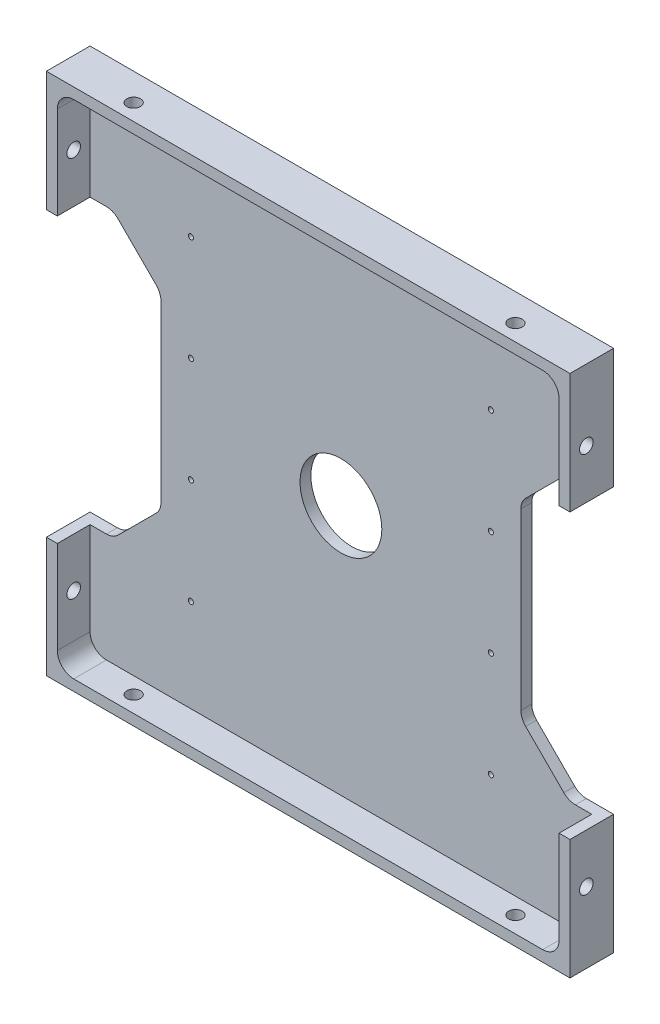
SolidWorks part; units mm, degrees
material "6061-T6 (SS)"
ref_plane "Front" through (0, 0, 0) normal (0, 0, 1) x (1, 0, 0)
ref_plane "Top" through (0, 0, 0) normal (0, 1, 0) x (1, 0, 0)
ref_plane "Right" through (0, 0, 0) normal (1, 0, 0) x (0, 0, -1)
sketch "Sketch1" plane through (0, 0, 0) normal (0, 0, 1) x (1, 0, 0)
  line L1 (-48, -48) -> (48, -48)
  line L2 (-48, -48) -> (-48, 48)
  line L3 (-48, 48) -> (48, 48)
  line L4 (48, -48) -> (48, 48)
  line L5 (-48, -48) -> (48, 48) construction
  line L6 (-48, 48) -> (48, -48) construction
  point P0 (0, 0)
  dimension "D1" = 96
  dimension "D2" = 96
extrude "Boss-Extrude1" add sketch "Sketch1" along normal blind 8
sketch "Sketch2" plane through (0, 0, 8) normal (0, 0, 1) x (1, 0, 0)
  line L1 (46, -46) -> (-46, -46)
  line L2 (46, -46) -> (46, 46)
  line L3 (46, 46) -> (-46, 46)
  line L4 (-46, -46) -> (-46, 46)
  line L5 (46, -46) -> (-46, 46) construction
  line L6 (46, 46) -> (-46, -46) construction
  point P0 (0, 0)
  dimension "D1" = 92
  dimension "D2" = 92
extrude "Component Platform" cut sketch "Sketch2" against normal blind 6
sketch "Sketch3" plane through (0, 0, 2) normal (0, 0, 1) x (1, 0, 0)
  line L1 (-40.8787, -25.1213) -> (-33.8787, -18.1213)
  line L2 (-40.8787, 25.1213) -> (-33.8787, 18.1213)
  line L3 (-33, -16) -> (-33, 16)
  line L4 (-48, -26) -> (-43, -26)
  line L7 (-48, 48) -> (-48, -48) construction
  line L8 (0, -56.7987) -> (0, 73.4321) construction
  line L9 (46, -46) -> (-57.8147, 57.8147) construction
  line L18 (46, 46) -> (-68.5705, -68.5705) construction
  line L23 (-48, 26) -> (-43, 26)
  line L26 (-48, -26) -> (-48, 26)
  line L28 (-48, -48) -> (48, -48) construction
  line L29 (48, -26) -> (48, 26)
  line L30 (48, 26) -> (43, 26)
  line L31 (40.8787, 25.1213) -> (33.8787, 18.1213)
  line L32 (33, -16) -> (33, 16)
  line L33 (40.8787, -25.1213) -> (33.8787, -18.1213)
  line L34 (48, -26) -> (43, -26)
  arc A3 (-33.8787, -18.1213) -> (-33, -16) centre (-36, -16) ccw
  arc A4 (-33.8787, 18.1213) -> (-33, 16) centre (-36, 16) cw
  arc A13 (-40.8787, -25.1213) -> (-43, -26) centre (-43, -23) cw
  arc A15 (-40.8787, 25.1213) -> (-43, 26) centre (-43, 23) ccw
  arc A17 (40.8787, 25.1213) -> (43, 26) centre (43, 23) cw
  arc A18 (33.8787, 18.1213) -> (33, 16) centre (36, 16) ccw
  arc A19 (33.8787, -18.1213) -> (33, -16) centre (36, -16) cw
  arc A20 (40.8787, -25.1213) -> (43, -26) centre (43, -23) ccw
  point P0 (-48, 0)
  point P37 (-48, 0)
  dimension "D2" = 3
  dimension "D3" = 3
  dimension "D4" = 15
  dimension "D6" = 3
  dimension "D7" = 3
  dimension "D8" = 135
  dimension "D5" = 52
  dimension "D9" = 135
  dimension "D10" = 5
  dimension "D11" = 5
  dimension "D12" = 48
extrude "Cable Slots" cut sketch "Sketch3" against normal mid plane 12
sketch "Sketch4" plane through (0, 0, 2) normal (0, 0, 1) x (1, 0, 0)
  circle A0 centre (0, 0) radius 7.5
  dimension "D1" = 15
extrude "Center Mass Cut" cut sketch "Sketch4" against normal blind 6
ref_plane "Center Y-Plane" through (0, 0, 0) normal (1, 0, 0) x (0, 0, -1)
ref_plane "Center X-Plane" through (0, 0, 0) normal (0, -1, 0) x (-1, 0, 0)
fillet "Inner Corner Fillets" radius 3 4 edges at (46, -46, 5) (-46, -46, 5) (46, 46, 5) (-46, 46, 5)
sketch "Sketch8" plane through (48, 0, 0) normal (1, 0, 0) x (0, 0, -1)
  line L0 (-5, -48) -> (-5, 48) construction
  line L1 (-8, -48) -> (0, -48) construction
  line L2 (-8, 48) -> (0, 48) construction
  line L3 (-8, -48) -> (-8, -26) construction
  point P12 (-5, 35)
  point P13 (-5, -35)
  dimension "D1" = 3
  dimension "D2" = 13
  dimension "D3" = 83
sketch "Sketch11" plane through (0, -48, 0) normal (0, -1, 0) x (-1, 0, 0)
  line L0 (48, -5) -> (-48.0639, -5) construction
  line L1 (48, -8) -> (48, 0) construction
  line L2 (48, -8) -> (-48, -8) construction
  dimension "D1" = 3
hole_wizard "Tap Drill for M3x0.5 Tap4" positions "Sketch12" profile "Sketch13" hole size "M3x0.5" standard "ANSI Metric" end condition up to next
sketch "Sketch12" plane through (0, -48, 0) normal (0, -1, 0) x (-1, 0, 0)
  line L0 (48, -5) -> (-48.0639, -5) construction
  point P0 (35, -5)
  point P4 (-35, -5)
  dimension "D1" = 70
  dimension "D2" = 35
sketch "Sketch13" plane through (-35, -48, 5) normal (1, 0, 0) x (0, 0, -1)
  line L0 (0, 0) -> (0, 2)
  line L1 (0, 2) -> (1.25, 2)
  line L2 (1.25, 2) -> (1.25, 0)
  line L5 (1.25, 0) -> (0, 0)
  line L11 (0, -6.35) -> (0, 107.95) construction
  dimension "Thru Hole Dia." = 2.5
  dimension "Thru Hole Depth" = 2
mirror "Mirror2" about plane through (0, 0, 0) normal (0, -1, 0) of "Tap Drill for M3x0.5 Tap4"
sketch "Sketch14" plane through (0, 0, 2) normal (0, 0, 1) x (1, 0, 0)
  line L2 (-34.3786, 28.95) -> (20.4987, 28.95) construction
  line L4 (-27.5, 33.479) -> (-27.5, -23.7116) construction
  line L5 (0, 0) -> (0, 28.95) construction
  point P7 (-27.5, 28.95)
  point P8 (-27.5, -9.65)
  point P9 (-27.5, 9.65)
  point P11 (-27.5, -28.95)
  point P13 (27.5, -28.95)
  point P14 (27.5, -9.65)
  point P15 (27.5, 9.65)
  point P16 (27.5, 28.95)
  dimension "D1" = 27.5
  dimension "D2" = 28.95
  dimension "D3" = 19.3
  dimension "D4" = 19.3
  dimension "D5" = 19.3
hole_wizard "Tap Drill for M1.2x0.25 Tap1" positions "Sketch15" profile "Sketch17" hole size "M1.2x0.25" standard "ANSI Metric" end condition through all
sketch "Sketch15" plane through (0, 0, 2) normal (0, 0, 1) x (1, 0, 0)
  point P0 (-27.5, 28.95)
  point P3 (-27.5, 9.65)
  point P6 (-27.5, -9.65)
  point P9 (-27.5, -28.95)
  point P12 (27.5, -28.95)
  point P15 (27.5, -9.65)
  point P18 (27.5, 9.65)
  point P21 (27.5, 28.95)
sketch "Sketch17" plane through (-27.5, 28.95, 2) normal (1, 0, 0) x (0, -1, 0)
  line L0 (0, 0) -> (0, 2)
  line L1 (0, 2) -> (0.475, 2)
  line L2 (0.475, 2) -> (0.475, 0)
  line L5 (0.475, 0) -> (0, 0)
  line L11 (0, -6.35) -> (0, 107.95) construction
  dimension "Thru Hole Dia." = 0.95
  dimension "Thru Hole Depth" = 2
hole_wizard "Tap Drill for M3x0.5 Tap3" positions "Sketch26" profile "Sketch27" hole size "M3x0.5" standard "ANSI Metric" end condition up to next
sketch "Sketch26" plane through (48, 0, 0) normal (1, 0, 0) x (0, 0, -1)
  point P0 (-5, -35)
  point P3 (-5, 35)
sketch "Sketch27" plane through (48, -35, 5) normal (0, 1, 0) x (0, 0, -1)
  line L0 (0, 0) -> (0, 2)
  line L1 (0, 2) -> (1.25, 2)
  line L2 (1.25, 2) -> (1.25, 0)
  line L5 (1.25, 0) -> (0, 0)
  line L11 (0, -6.35) -> (0, 107.95) construction
  dimension "Thru Hole Dia." = 2.5
  dimension "Thru Hole Depth" = 2
mirror "Mirror3" about plane through (0, 0, 0) normal (1, 0, 0) of "Tap Drill for M3x0.5 Tap3"
